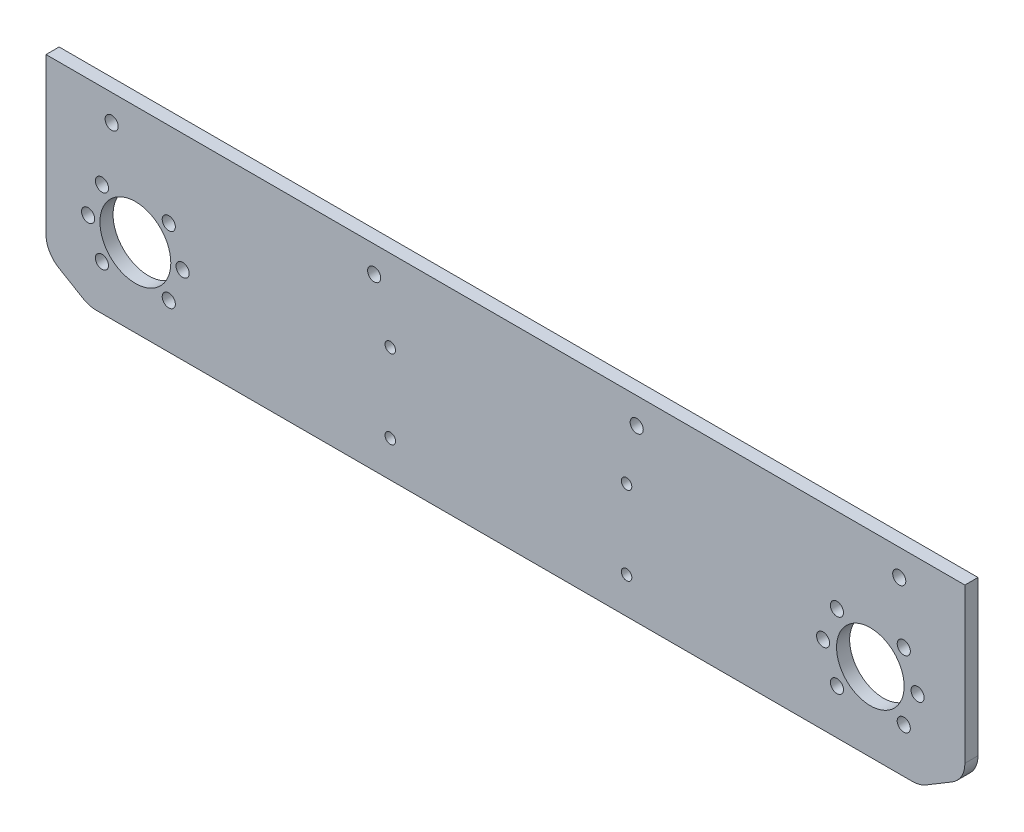
SolidWorks part; units mm, degrees
ref_plane "前基準面" through (0, 0, 0) normal (0, 0, 1) x (1, 0, 0)
ref_plane "上基準面" through (0, 0, 0) normal (0, 1, 0) x (1, 0, 0)
ref_plane "右基準面" through (0, 0, 0) normal (1, 0, 0) x (0, 0, -1)
sketch "草圖1" plane through (0, 0, 0) normal (0, 0, 1) x (1, 0, 0)
  line L1 (-177.4028, 46.5972) -> (172.5972, 46.5972)
  line L2 (-177.4028, 46.5972) -> (-177.4028, -3.2183)
  line L4 (172.5972, 46.5972) -> (172.5972, -3.2183)
  line L27 (-177.4028, -10.3077) -> (-177.4028, -12.7734)
  line L29 (-177.4028, -3.2183) -> (-177.4028, -10.3077)
  line L31 (172.5972, -12.2123) -> (172.5972, -3.2183)
  line L33 (-172.4854, -21.3854) -> (-163.2874, -26.8139)
  line L34 (-158.2047, -28.2019) -> (152.6198, -28.2019)
  line L35 (157.7668, -26.7756) -> (167.7442, -20.786)
  circle A0 centre (118.5902, 1.6361) radius 2.5
  circle A1 centre (154.5902, 1.6361) radius 2.5
  circle A2 centre (136.5902, 1.6361) radius 12.875
  circle A4 centre (-143.3646, 1.6161) radius 13.5
  circle A9 centre (-130.6367, 14.3441) radius 2.5
  circle A10 centre (-156.0926, 14.3441) radius 2.5
  circle A11 centre (-130.6367, -11.1118) radius 2.5
  circle A12 centre (-156.0926, -11.1118) radius 2.5
  circle A30 centre (-152.4028, 36.5972) radius 2.5
  circle A31 centre (-52.4028, 36.5972) radius 2.5
  circle A32 centre (47.5972, 36.5972) radius 2.5
  circle A33 centre (147.5972, 36.5972) radius 2.5
  arc A35 (-163.2874, -26.8139) -> (-158.2047, -28.2019) centre (-158.2047, -18.2019) ccw
  arc A36 (-172.4854, -21.3854) -> (-177.4028, -12.7734) centre (-167.4028, -12.7734) cw
  arc A37 (167.7442, -20.786) -> (172.5972, -12.2123) centre (162.5972, -12.2123) ccw
  arc A38 (157.7668, -26.7756) -> (152.6198, -28.2019) centre (152.6198, -18.2019) cw
  circle A39 centre (-161.3646, 1.6161) radius 2.5
  circle A40 centre (-125.3646, 1.6161) radius 2.5
  circle A41 centre (149.3181, -11.0919) radius 2.5
  circle A42 centre (123.8623, -11.0919) radius 2.5
  circle A43 centre (123.8623, 14.364) radius 2.5
  circle A44 centre (149.3181, 14.364) radius 2.5
  circle A46 centre (-46.269, 15.5908) radius 2
  circle A47 centre (-46.269, -14.4092) radius 2
  circle A48 centre (43.7374, 15.5908) radius 2
  circle A49 centre (43.7374, -14.4092) radius 2
  point P0 (0, 0)
  dimension "D5" = 5
  dimension "D10" = 27
  dimension "D11" = 34.0381
  dimension "D12" = 44.9811
  dimension "D13" = 18
  dimension "D20" = 4
  dimension "D21" = 10
  dimension "D22" = 25.75
  dimension "D26" = 10
  dimension "D28" = 18
  dimension "D1" = 350
  dimension "D6" = 44.9612
  dimension "D7" = 36
extrude "填料-伸長1" add sketch "草圖1" along normal blind 5
